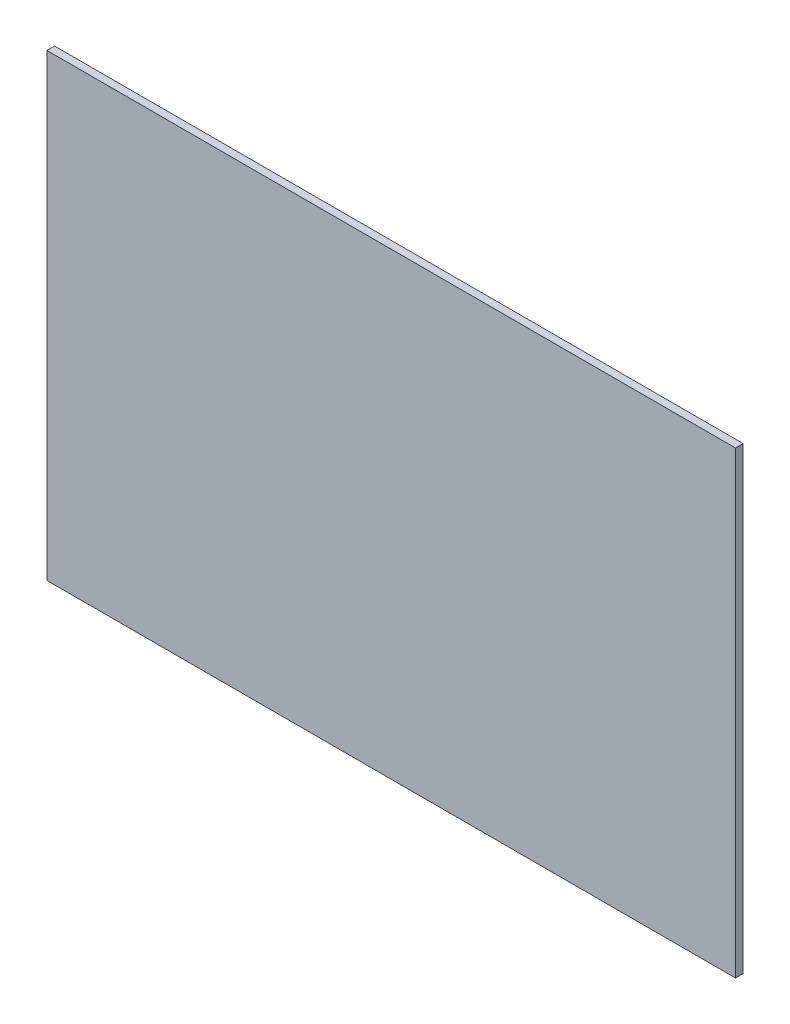
SolidWorks part; units mm, degrees
ref_plane "Plan de face" through (0, 0, 0) normal (0, 0, 1) x (1, 0, 0)
ref_plane "Plan de dessus" through (0, 0, 0) normal (0, 1, 0) x (1, 0, 0)
ref_plane "Plan de droite" through (0, 0, 0) normal (1, 0, 0) x (0, 0, -1)
sketch "Esquisse1" plane through (0, 0, 0) normal (0, 0, 1) x (1, 0, 0)
  line L1 (-65.6501, 67.6742) -> (204.3499, 67.6742)
  line L2 (-65.6501, 67.6742) -> (-65.6501, -112.3258)
  line L3 (-65.6501, -112.3258) -> (204.3499, -112.3258)
  line L4 (204.3499, 67.6742) -> (204.3499, -112.3258)
  dimension "D1" = 270
  dimension "D2" = 180
extrude "Boss.-Extru.1" add sketch "Esquisse1" along normal blind 3
equation "\"D1@Esquisse1\"=\"LongueurSyphon\""
equation "\"D2@Esquisse1\"=\"HauteurSyphon\"-60"
equation "\"ProfondeurBoite\"=460"
equation "\"LongueurSyphon\"=270"
equation "\"LargeurSyphon\"=120"
equation "\"EpaisseurPlaque\"= 3"
equation "\"HauteurSyphon\"=\"HauteurCoteGauche\"-\"HauteurSolSyphon\""
equation "\"D1@Boss.-Extru.1\"=\"EpaisseurPlaque\""
equation "\"HauteurCoteDroit\"= 490"
equation "\"HauteurCoteGauche\"= 540"
equation "\"HauteurSolSyphon\"= 300"
equation "\"LargeurDroite\"=10"
equation "\"LargeurGauche\"=150"
equation "\"LargeurBoite\"= \"LargeurDroite\" + \"LargeurGauche\" + \"LargeurSyphon\""
